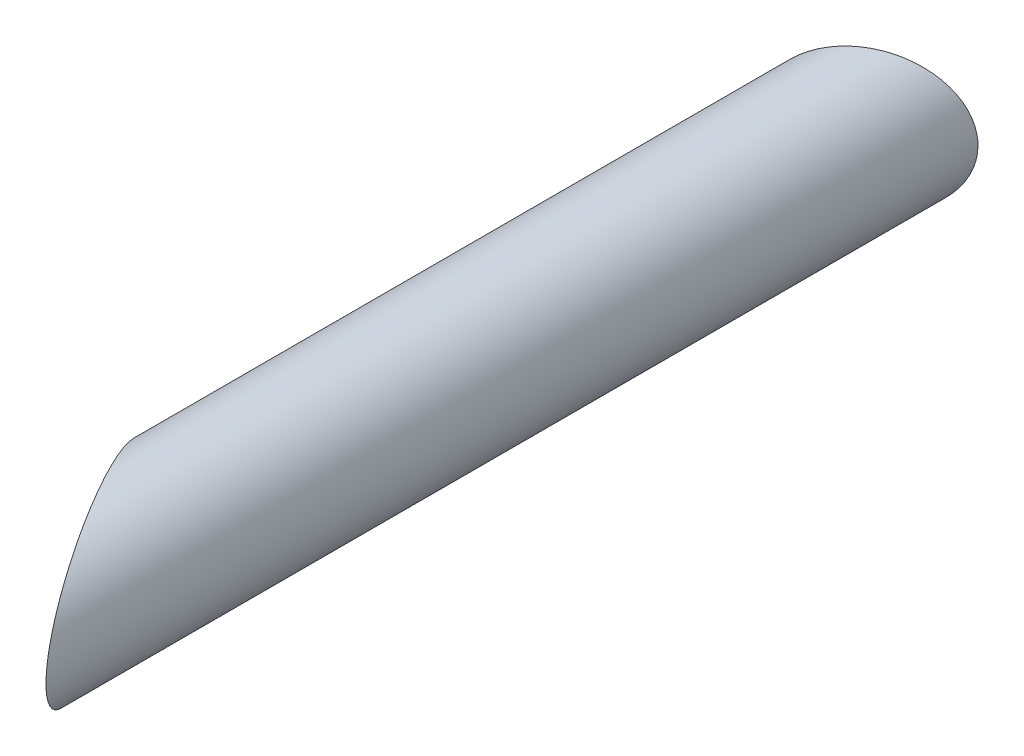
SolidWorks part; units mm, degrees
material "Oak"
ref_plane "Front Plane" through (0, 0, 0) normal (0, 0, 1) x (1, 0, 0)
ref_plane "Top Plane" through (0, 0, 0) normal (0, 1, 0) x (1, 0, 0)
ref_plane "Right Plane" through (0, 0, 0) normal (1, 0, 0) x (0, 0, -1)
sketch "Sketch1" plane through (0, 0, 0) normal (0, 0, 1) x (1, 0, 0)
  circle A0 centre (0, 0) radius 7.5
  dimension "D1" = 15
extrude "Boss-Extrude1" add sketch "Sketch1" along normal blind 100
sketch "Sketch5" plane through (0, 0, 0) normal (0, 1, 0) x (1, 0, 0)
  line L0 (7.5, 0) -> (-7.5, -8.6603)
  line L1 (-7.5, 0) -> (-7.5, -100) construction
  line L2 (7.5, 0) -> (-7.5, 0) construction
  line L3 (-7.5, -8.6603) -> (-7.5, 0)
  line L4 (-7.5, 0) -> (7.5, 0)
  line L5 (7.5, -100) -> (-4.9221, -78.4843)
  line L6 (-7.5, -100) -> (7.5, -100) construction
  line L7 (-4.9221, -78.4843) -> (-7.5, -74.0192)
  line L8 (-7.5, -74.0192) -> (-7.5, -100)
  line L9 (-7.5, -100) -> (7.5, -100)
  dimension "D1" = 30
  dimension "D2" = 60
extrude "Cut-Extrude1" cut sketch "Sketch5" along normal through all both and the other way through all
sketch "Sketch19" plane through (1.875, 0, 3.2476) normal (-0.5, 0, -0.866) x (-0.866, 0, 0.5)
  line L0 (-6.4952, 0) -> (10.8253, 0) construction
  ellipse E1 centre (2.1651, 0) end of major axis (-6.4952, 0) minor radius 7.5
  ellipse E2 centre (2.1651, 0) end of major axis (-6.4952, 0) minor radius 7.5 construction
  point P0 (4.8253, 0)
  dimension "D2" = 6
  dimension "D1" = 0
hole_wizard "M5x0.8 Tapped Hole2" positions "Sketch19" profile "Sketch20" tap size "M5x0.8" standard "ANSI Metric"
sketch "Sketch20" plane through (-2.3038, 0, 5.6603) normal (0, 1, 0) x (-0.866, 0, 0.5)
  line L0 (0, 0) -> (0, 11.2618)
  line L1 (0, 11.2618) -> (2.1, 10)
  line L2 (2.1, 10) -> (2.1, 0)
  line L5 (2.1, 0) -> (0, 0)
  line L10 (0, 11.2618) -> (-2.1, 10) construction
  line L11 (0, -6.35) -> (0, 107.95) construction
  dimension "Tap Drill Dia." = 4.2
  dimension "Tap Drill Depth" = 10
  dimension "Drill Angle" = 118
cosmetic thread "Hole Thread4" parameters "D1"=8, "D2"=5
sketch "Sketch21" plane through (-37.6763, 0, 21.7524) normal (-0.866, 0, 0.5) x (0.5, 0, 0.866)
  ellipse E0 centre (75.3525, 0) end of major axis (60.3525, 0) minor radius 7.5 construction
  ellipse E1 centre (75.3525, 0) end of major axis (90.3525, 0) minor radius 7.5 construction
  point P0 (68.3525, 0)
  dimension "D1" = 8
hole_wizard "M5x0.8 Tapped Hole3" positions "Sketch21" profile "Sketch22" tap size "M5x0.8" standard "ANSI Metric"
sketch "Sketch22" plane through (-3.5, 0, 80.9474) normal (0, 1, 0) x (0.5, 0, 0.866)
  line L0 (0, 0) -> (0, 8.2618)
  line L1 (0, 8.2618) -> (2.1, 7)
  line L2 (2.1, 7) -> (2.1, 0)
  line L5 (2.1, 0) -> (0, 0)
  line L10 (0, 8.2618) -> (-2.1, 7) construction
  line L11 (0, -6.35) -> (0, 107.95) construction
  dimension "Tap Drill Dia." = 4.2
  dimension "Tap Drill Depth" = 7
  dimension "Drill Angle" = 118
cosmetic thread "Hole Thread5" parameters "D1"=5, "D2"=5
